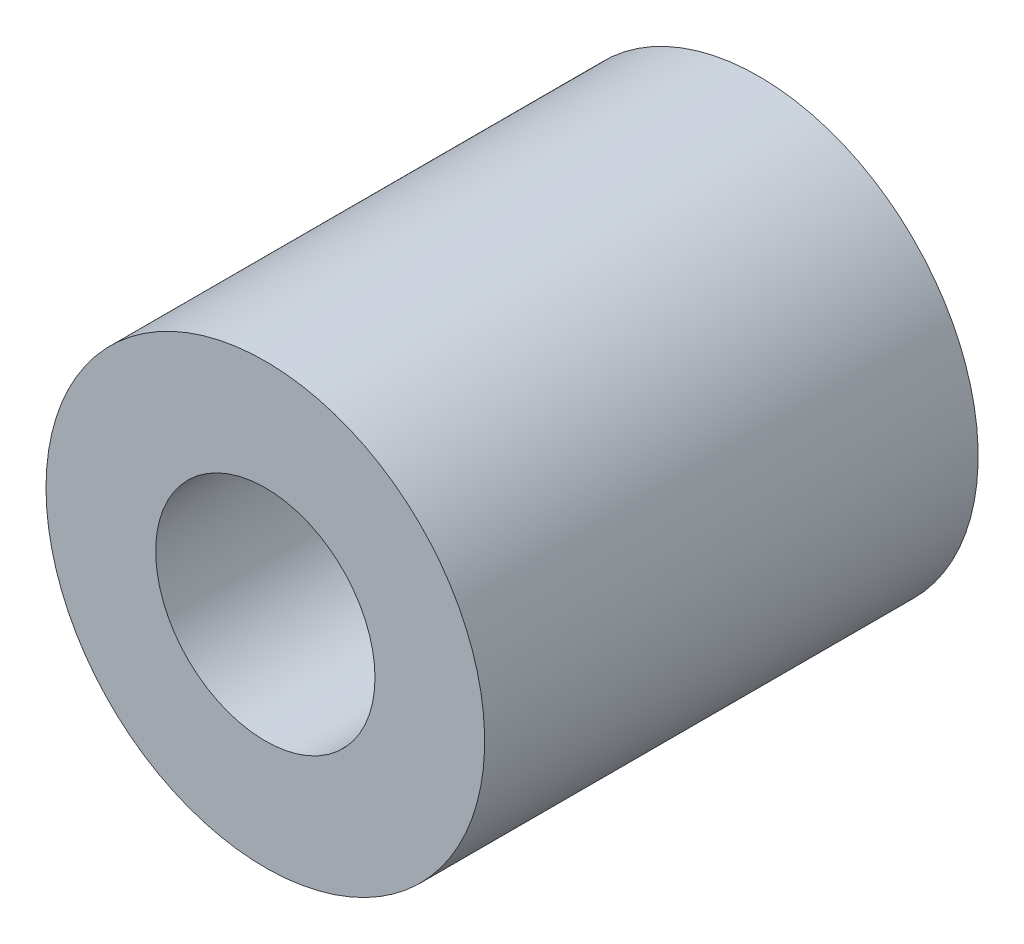
SolidWorks part; units mm, degrees
ref_plane "正面" through (0, 0, 0) normal (0, 0, 1) x (1, 0, 0)
ref_plane "平面" through (0, 0, 0) normal (0, 1, 0) x (1, 0, 0)
ref_plane "右側面" through (0, 0, 0) normal (1, 0, 0) x (0, 0, -1)
sketch "ｽｹｯﾁ1" plane through (0, 0, 0) normal (0, 0, 1) x (1, 0, 0)
  circle A0 centre (0, 0) radius 2
  circle A1 centre (0, 0) radius 5 construction
  circle A2 centre (0, 0) radius 4
  dimension "D2" = 4
  dimension "D3" = 8
extrude "ﾎﾞｽ - 押し出し1" add sketch "ｽｹｯﾁ1" along normal blind 9
